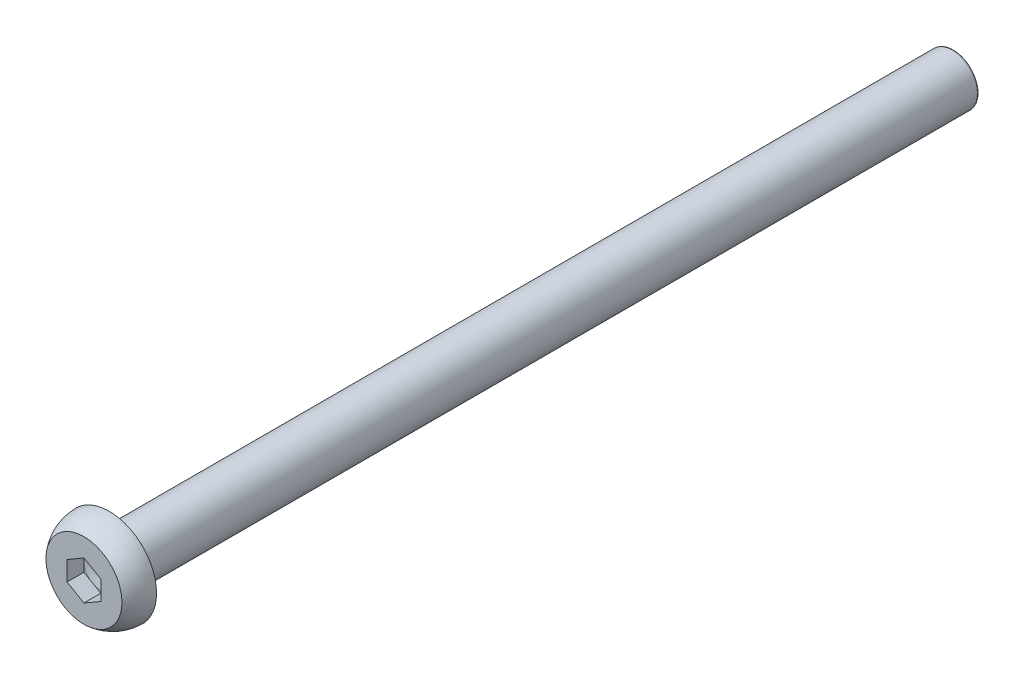
SolidWorks part; units mm, degrees
ref_plane "前视基准面" through (0, 0, 0) normal (0, 0, 1) x (1, 0, 0)
ref_plane "上视基准面" through (0, 0, 0) normal (0, 1, 0) x (1, 0, 0)
ref_plane "右视基准面" through (0, 0, 0) normal (1, 0, 0) x (0, 0, -1)
sketch "草图1" plane through (0, 0, 0) normal (1, 0, 0) x (0, 0, -1)
  line L4 (0, 2.2503) -> (0, 1)
  line L6 (1, 1) -> (1.2482, 0)
  line L9 (1.5, 1.5) -> (51.5, 1.5)
  line L10 (51.5, 1.5) -> (51.5, 0)
  line L12 (1.5, 2.8) -> (1.5, 1.5)
  line L13 (0, 0) -> (1.5, 0) construction
  line L14 (1.2482, 0) -> (51.5, 0)
  line L15 (0, 1) -> (0, 0)
  line L16 (0, 0) -> (1, 0)
  line L17 (1, 0) -> (1, 1)
  arc A0 (1.5, 2.8) -> (0, 2.2503) centre (1.5, 0.4784) ccw
revolve "旋转2" add sketch "草图1" angle 360 about L13
sketch "草图2" plane through (0, 0, 0) normal (0, 0, 1) x (1, 0, 0)
  line L1 (0, 1.1547) -> (-1, 0.5774)
  line L2 (-1, 0.5774) -> (-1, -0.5774)
  line L3 (-1, -0.5774) -> (0, -1.1547)
  line L4 (0, -1.1547) -> (1, -0.5774)
  line L5 (1, -0.5774) -> (1, 0.5774)
  line L6 (1, 0.5774) -> (0, 1.1547)
  circle A0 centre (0, 0) radius 1 construction
  dimension "D1" = 2
extrude "切除-拉伸1" cut sketch "草图2" against normal blind 1
fillet "圆角1" radius 0.1 1 edges at (1.5, 0, -51.5)
